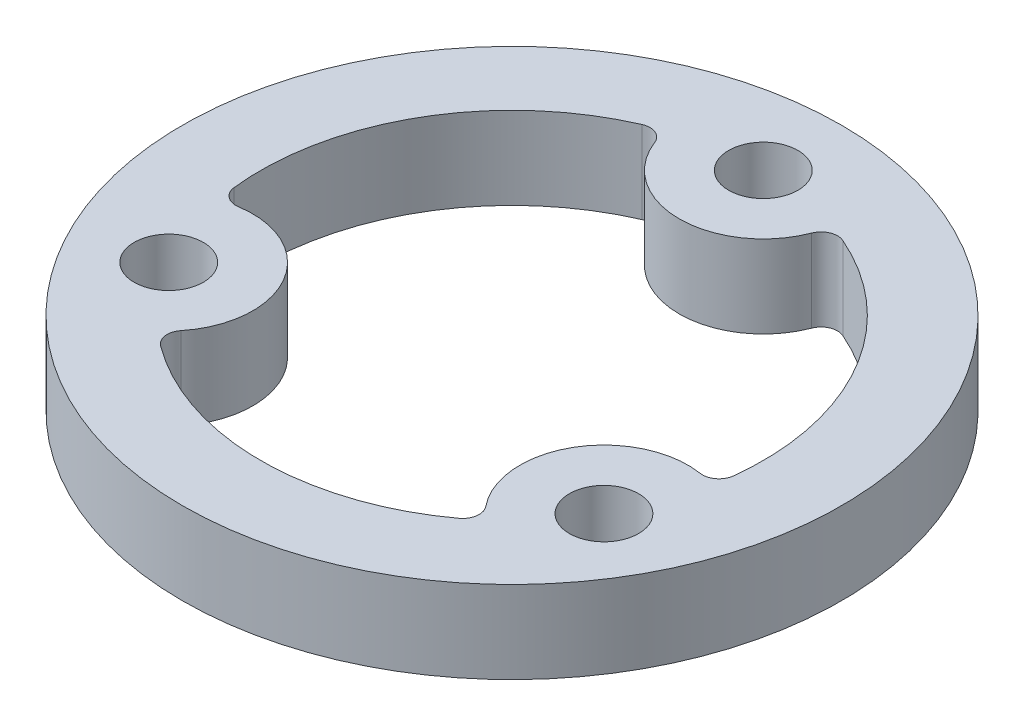
SolidWorks part; units mm, degrees
ref_plane "Front Plane" through (0, 0, 0) normal (0, 0, 1) x (1, 0, 0)
ref_plane "Top Plane" through (0, 0, 0) normal (0, 1, 0) x (1, 0, 0)
ref_plane "Right Plane" through (0, 0, 0) normal (1, 0, 0) x (0, 0, -1)
sketch "Sketch1" plane through (0, 0, 0) normal (0, 1, 0) x (1, 0, 0)
  circle A0 centre (0, 0) radius 10
  circle A1 centre (0, 0) radius 20
  circle A2 centre (0, 0) radius 15.25 construction
  circle A3 centre (0, 15.25) radius 2.1
  circle A6 centre (13.2069, -7.625) radius 2.1
  circle A7 centre (-13.2069, -7.625) radius 2.1
  point P13 (0, 0)
  dimension "D1" = 20
  dimension "D2" = 40
  dimension "D3" = 30.5
  dimension "D4" = 4.2
  dimension "D5" = 3
extrude "Boss-Extrude1" add sketch "Sketch1" along normal blind 5
sketch "Sketch2" plane through (0, 5, 0) normal (0, 1, 0) x (1, 0, 0)
  arc A0 (-5.0282, 14.3972) -> (5.0282, 14.3972) centre (0, 15.25) ccw
  arc A1 (14.9825, -2.8441) -> (9.9543, -11.5532) centre (13.2069, -7.625) ccw
  arc A2 (-9.9543, -11.5532) -> (-14.9825, -2.8441) centre (-13.2069, -7.625) ccw
  arc A3 (-5.0282, 14.3972) -> (-14.9825, -2.8441) centre (0, 0) ccw
  circle A4 centre (0, 15.25) radius 2.1 construction
  arc A5 (-9.9543, -11.5532) -> (9.9543, -11.5532) centre (0, 0) ccw
  arc A6 (14.9825, -2.8441) -> (5.0282, 14.3972) centre (0, 0) ccw
  dimension "D1" = 3
extrude "Cut-Extrude1" cut sketch "Sketch2" against normal through all
fillet "Fillet1" radius 1 6 edges at (-9.9543, 2.5, 11.5532) (-14.9825, 2.5, 2.8441) (9.9543, 2.5, 11.5532) (14.9825, 2.5, 2.8441) (5.0282, 2.5, -14.3972) (-5.0282, 2.5, -14.3972)
